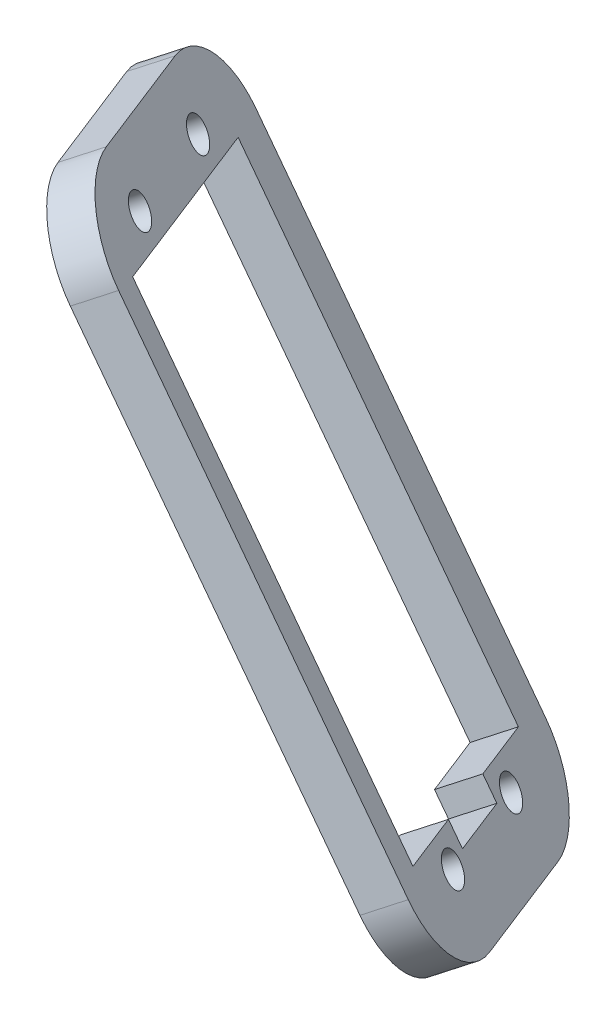
SolidWorks part; units mm, degrees
material "Acrylic (Medium-high impact)"
ref_plane "Front Plane" through (0, 0, 0) normal (0, 0, 1) x (1, 0, 0)
ref_plane "Top Plane" through (0, 0, 0) normal (0, 1, 0) x (1, 0, 0)
ref_plane "Right Plane" through (0, 0, 0) normal (1, 0, 0) x (0, 0, -1)
sketch "Sketch1" plane through (-134.332, -86.2627, 84.9919) normal (-0.7427, -0.477, 0.4699) x (0.3954, 0.2539, 0.8827)
  line L1 (-449.9601, 72.0735) -> (-410.1587, 68.092)
  line L2 (-449.9601, 72.0735) -> (-458.1223, -9.5192)
  line L3 (-458.1223, -9.5192) -> (-418.3209, -13.5008)
  line L4 (-410.1587, 68.092) -> (-418.3209, -13.5008)
  line B0 (-431.103, -0.4686) -> (-420.8044, -1.4988)
  line B1 (-451.3519, 1.5571) -> (-445.3796, 61.2591)
  line B2 (-451.3519, 1.5571) -> (-441.0533, 0.5268)
  line B3 (-420.8044, -1.4988) -> (-414.832, 58.2032)
  line B4 (-445.3796, 61.2591) -> (-414.832, 58.2032)
  line B5 (-441.0533, 0.5268) -> (-441.3519, -2.4583)
  line B6 (-431.103, -0.4686) -> (-431.4016, -3.4537)
  line B7 (-441.3519, -2.4583) -> (-431.4016, -3.4537)
sketch_block_instance "servo-1"
sketch_block "servo" parameters "D1"=60, "D2"=30.7, "D3"=10, "D4"=3
extrude "Boss-Extrude1" add sketch "Sketch1" along normal blind 5
sketch "Sketch2" plane through (-138.0457, -88.6475, 87.3416) normal (-0.7427, -0.477, 0.4699) x (0.3954, 0.2539, 0.8827)
  circle A0 centre (-444.8346, -2.6124) radius 2
  circle A1 centre (-428.0185, -4.2946) radius 2
  circle A2 centre (-438.1654, 64.0549) radius 2
  circle A3 centre (-421.3494, 62.3727) radius 2
extrude "Cut-Extrude1" cut sketch "Sketch2" against normal blind 10
fillet "Fillet1" radius 10 4 edges at (-294.3081, -205.0377, -283.0856) (-312.1979, -211.7941, -318.2183) (-335.1686, -134.3093, -275.8808) (-353.0584, -141.0656, -311.0135)
